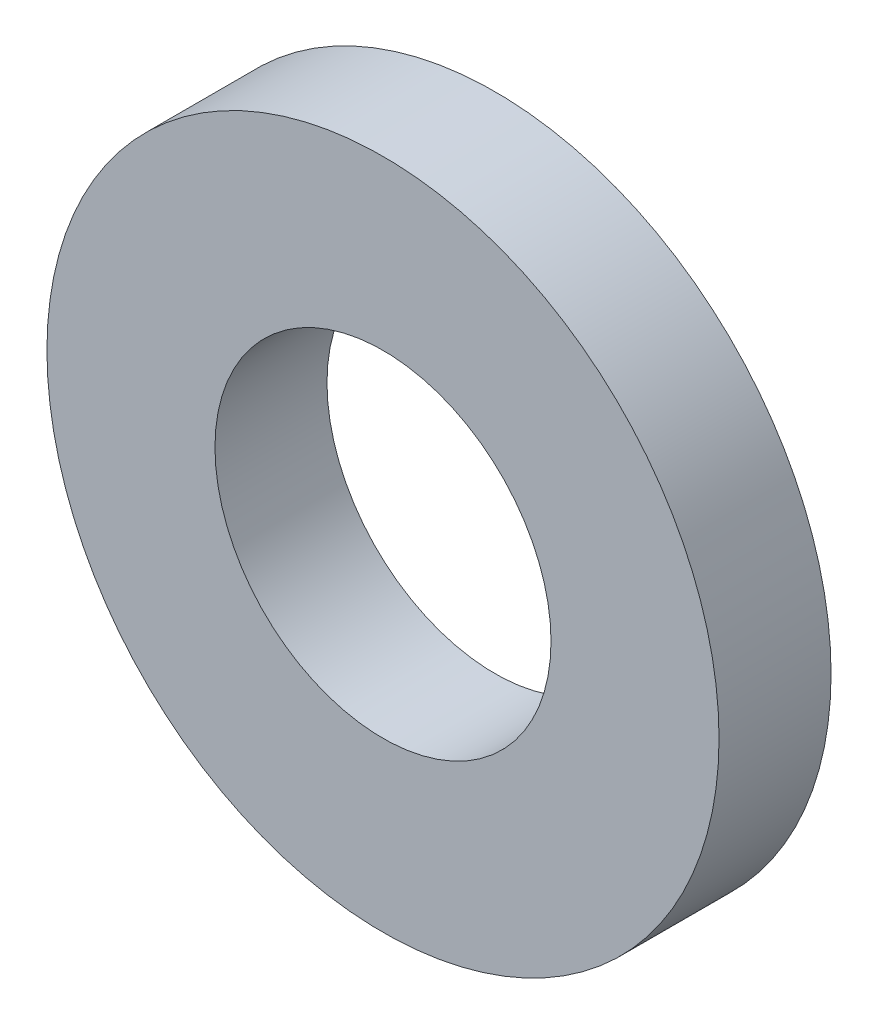
SolidWorks part; units mm, degrees
ref_plane "Plan de face" through (0, 0, 0) normal (0, 0, 1) x (1, 0, 0)
ref_plane "Plan de dessus" through (0, 0, 0) normal (0, 1, 0) x (1, 0, 0)
ref_plane "Plan de droite" through (0, 0, 0) normal (1, 0, 0) x (0, 0, -1)
sketch "Esquisse1" plane through (0, 0, 0) normal (0, 0, 1) x (1, 0, 0)
  circle A0 centre (0, 0) radius 3
  circle A1 centre (0, 0) radius 6
  dimension "D1" = 6
  dimension "D2" = 3
extrude "Boss.-Extru.1" add sketch "Esquisse1" along normal blind 2
